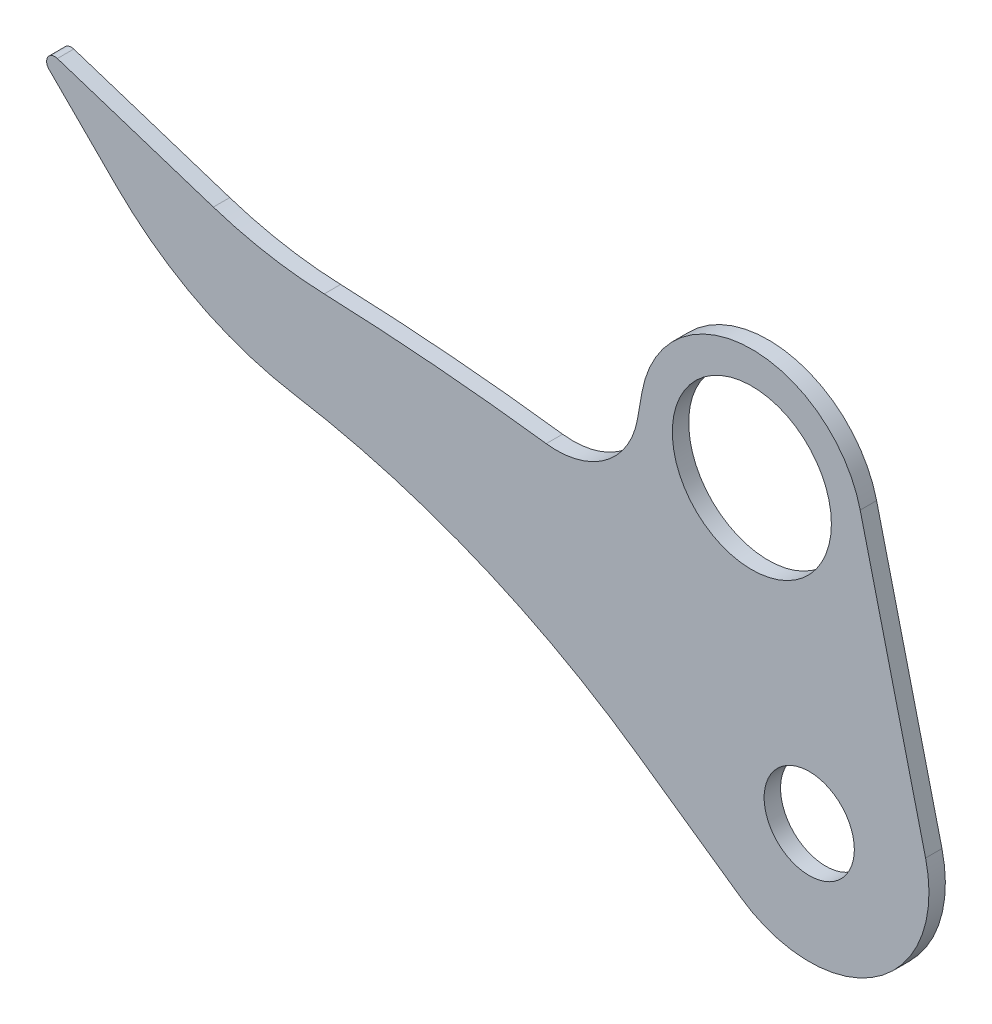
SolidWorks part; units mm, degrees
ref_plane "Plane1" through (0, 0, 0) normal (0, 0, 1) x (1, 0, 0)
ref_plane "Plane2" through (0, 0, 0) normal (0, 1, 0) x (1, 0, 0)
ref_plane "Plane3" through (0, 0, 0) normal (1, 0, 0) x (0, 0, -1)
sketch "Sketch1" plane through (0, 0, 0) normal (0, 0, 1) x (1, 0, 0)
  line L0 (70.9307, 17.258) -> (31.0724, 181.076)
  line L1 (-101.9669, 176.8081) -> (-104.6983, 161.3176)
  line L3 (-35, 165) -> (-303.9, 165) construction
  line L5 (-422.5161, 125.445) -> (-463.5355, 166.4645)
  line L6 (-41.8711, -59.7981) -> (-104.3289, -16.0647)
  line L7 (-458.4549, 174.7553) -> (-363.3493, 143.8536)
  circle A0 centre (0, 0) radius 27.5
  arc A1 (-41.8711, -59.7981) -> (70.9307, 17.258) centre (0, 0) ccw
  arc A2 (31.0724, 181.076) -> (-101.9669, 176.8081) centre (-35, 165) ccw
  arc A3 (-160.3818, 120.4169) -> (-295.7493, 131.8042) centre (-353.6747, -1367.0769) ccw
  arc A4 (-104.3289, -16.0647) -> (-313.9333, 69.5807) centre (-398, -435.4705) ccw
  arc A5 (-313.9333, 69.5807) -> (-422.5161, 125.445) centre (-281.0948, 266.8664) cw
  arc A6 (-160.3818, 120.4169) -> (-104.6983, 161.3176) centre (-153.9387, 170) ccw
  arc A7 (-463.5355, 166.4645) -> (-458.4549, 174.7553) centre (-460, 170) cw
  circle A8 centre (-35, 165) radius 48.5
  arc A9 (-295.7493, 131.8042) -> (-363.3493, 143.8536) centre (-286.095, 381.6177) cw
  dimension "D1" = 73
  dimension "D2" = 55
  dimension "D3" = 35
  dimension "D4" = 97
  dimension "D5" = 165
  dimension "D6" = 68
  dimension "D7" = 35
  dimension "D9" = 18
  dimension "D10" = 1500
  dimension "D11" = 250
  dimension "D15" = 100
  dimension "D16" = 5
  dimension "D17" = 512
  dimension "D18" = 200
  dimension "D13" = 170
  dimension "D14" = 50
  dimension "D12" = 306
  dimension "D8" = 100
  dimension "D19" = 45
  dimension "D20" = 460
  dimension "D21" = 170
  dimension "D22" = 398
extrude "Base-Extrude" add sketch "Sketch1" along normal blind 10
